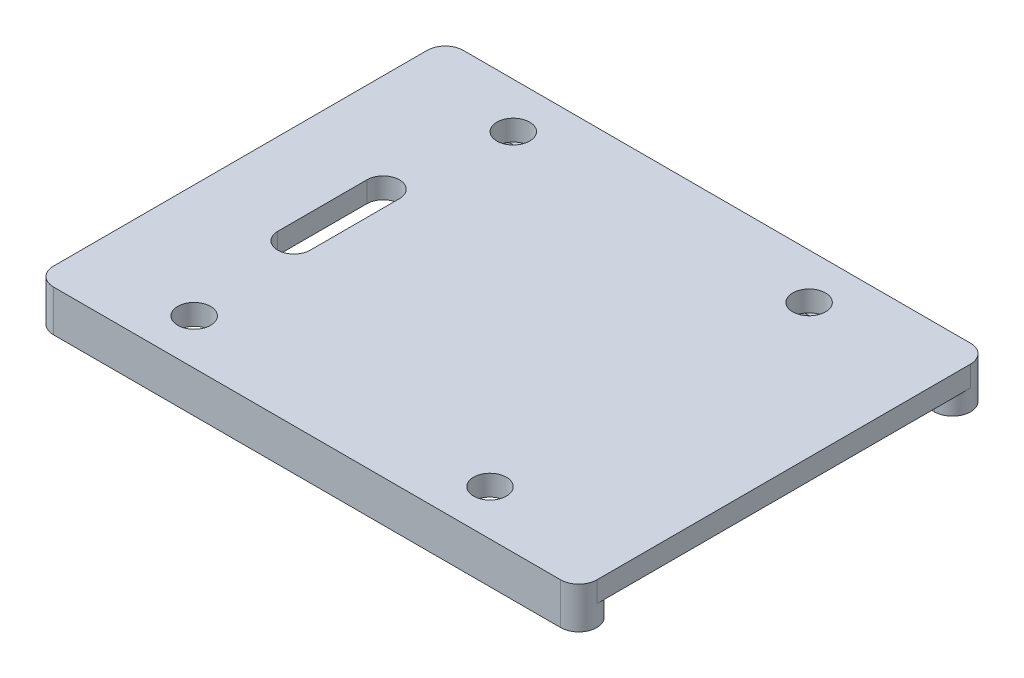
SolidWorks part; units mm, degrees
ref_plane "Alzado" through (0, 0, 0) normal (0, 0, 1) x (1, 0, 0)
ref_plane "Planta" through (0, 0, 0) normal (0, 1, 0) x (1, 0, 0)
ref_plane "Vista lateral" through (0, 0, 0) normal (1, 0, 0) x (0, 0, -1)
sketch "Croquis2" plane through (0, 19.0765, 0) normal (0, 1, 0) x (1, 0, 0)
  line L35 (29.003, 14.4708) -> (29.003, -42.77) construction
  line L36 (-22.997, 5.6441) -> (26.003, 5.6441)
  line L37 (-22.997, -33.9433) -> (26.003, -33.9433)
  line L38 (26.003, -30.4567) -> (-22.997, -30.4567)
  line L39 (-22.997, -33.9433) -> (26.003, -33.9433)
  line L40 (26.003, -30.4567) -> (-22.997, -30.4567)
  line L41 (26.003, 2.1575) -> (-22.997, 2.1575)
  line L42 (29.003, -14.1496) -> (-29.997, -14.1496) construction
  line L43 (-29.997, -42.77) -> (-29.997, 14.4708) construction
  arc A35 (-22.997, 2.1575) -> (-22.997, 5.6441) centre (-22.997, 3.9008) cw
  arc A36 (26.003, 5.6441) -> (26.003, 2.1575) centre (26.003, 3.9008) cw
  arc A37 (26.003, -33.9433) -> (26.003, -30.4567) centre (26.003, -32.2) ccw
  arc A38 (-22.997, -30.4567) -> (-22.997, -33.9433) centre (-22.997, -32.2) ccw
  arc A39 (26.003, -33.9433) -> (26.003, -30.4567) centre (26.003, -32.2) ccw
  arc A40 (-22.997, -30.4567) -> (-22.997, -33.9433) centre (-22.997, -32.2) ccw
  dimension "D1" = 0
extrude "Saliente-Extruir1" add sketch "Croquis2" against normal up to surface (2 mm away)
sketch "Croquis3" plane through (0, 19.0765, 0) normal (0, 1, 0) x (1, 0, 0)
  line L11 (-22.997, 2.1575) -> (26.003, 2.1575)
  line L12 (26.003, 5.6441) -> (-22.997, 5.6441)
  line L14 (26.003, 5.6441) -> (-22.997, 5.6441)
  line L17 (26.003, -30.4567) -> (-22.997, -30.4567)
  line L18 (-22.997, -33.9433) -> (26.003, -33.9433)
  line L20 (-22.997, -33.9433) -> (26.003, -33.9433)
  line L21 (-24.7403, 3.9008) -> (-24.7403, -32.2)
  line L23 (27.7463, 3.9008) -> (27.7463, -32.2)
  line L42 (-16.8212, -9.84) -> (-16.8212, -18.46)
  line L43 (-13.6728, -18.46) -> (-13.6728, -9.84)
  line L44 (-16.8212, -9.84) -> (-16.8212, -18.46)
  line L45 (-13.6728, -18.46) -> (-13.6728, -9.84)
  arc A4 (26.003, 2.1575) -> (26.003, 5.6441) centre (26.003, 3.9008) ccw
  arc A5 (27.7463, 3.9008) -> (26.003, 5.6441) centre (26.003, 3.9008) ccw
  arc A9 (-16.8212, -18.46) -> (-13.6728, -18.46) centre (-15.247, -18.46) ccw
  arc A10 (-13.6728, -9.84) -> (-16.8212, -9.84) centre (-15.247, -9.84) ccw
  arc A11 (-16.8212, -18.46) -> (-13.6728, -18.46) centre (-15.247, -18.46) ccw
  arc A12 (-13.6728, -9.84) -> (-16.8212, -9.84) centre (-15.247, -9.84) ccw
  arc A23 (-22.997, 5.6441) -> (-22.997, 2.1575) centre (-22.997, 3.9008) ccw
  arc A24 (26.003, 2.1575) -> (26.003, 5.6441) centre (26.003, 3.9008) ccw
  arc A25 (-22.997, 5.6441) -> (-24.7403, 3.9008) centre (-22.997, 3.9008) ccw
  arc A26 (27.7463, 3.9008) -> (26.003, 5.6441) centre (26.003, 3.9008) ccw
  arc A29 (26.003, -33.9433) -> (26.003, -30.4567) centre (26.003, -32.2) ccw
  arc A30 (-22.997, -30.4567) -> (-22.997, -33.9433) centre (-22.997, -32.2) ccw
  arc A31 (26.003, -33.9433) -> (27.7463, -32.2) centre (26.003, -32.2) ccw
  arc A32 (-24.7403, -32.2) -> (-22.997, -33.9433) centre (-22.997, -32.2) ccw
  arc M20 (-22.997, 5.6441) -> (-22.997, 2.1575) centre (-22.997, 3.9008) ccw
  line M21 (-22.997, 2.1575) -> (26.003, 2.1575)
  arc M22 (26.003, 2.1575) -> (26.003, 5.6441) centre (26.003, 3.9008) ccw
  line M23 (26.003, 5.6441) -> (-22.997, 5.6441)
  dimension "D1" = 0
  dimension "D2" = 0
  dimension "D3" = 0
  dimension "D4" = 0
extrude "Saliente-Extruir2" add sketch "Croquis3" along normal blind 2 contours L21 A32 L20 A31 L23 A12 L45 A11 L44 M22 M21 M20 | M23 M20 M21 M22
sketch "Croquis4" plane through (0, 21.0765, 0) normal (0, 1, 0) x (1, 0, 0)
  circle A0 centre (-13.7845, 1.2625) radius 1.5875
  circle A1 centre (14.7905, 1.2625) radius 1.5875
  circle A2 centre (14.7905, -29.5625) radius 1.5875
  circle A3 centre (-13.7845, -29.5625) radius 1.5875
extrude "Cortar-Extruir1" cut sketch "Croquis4" against normal blind 2
